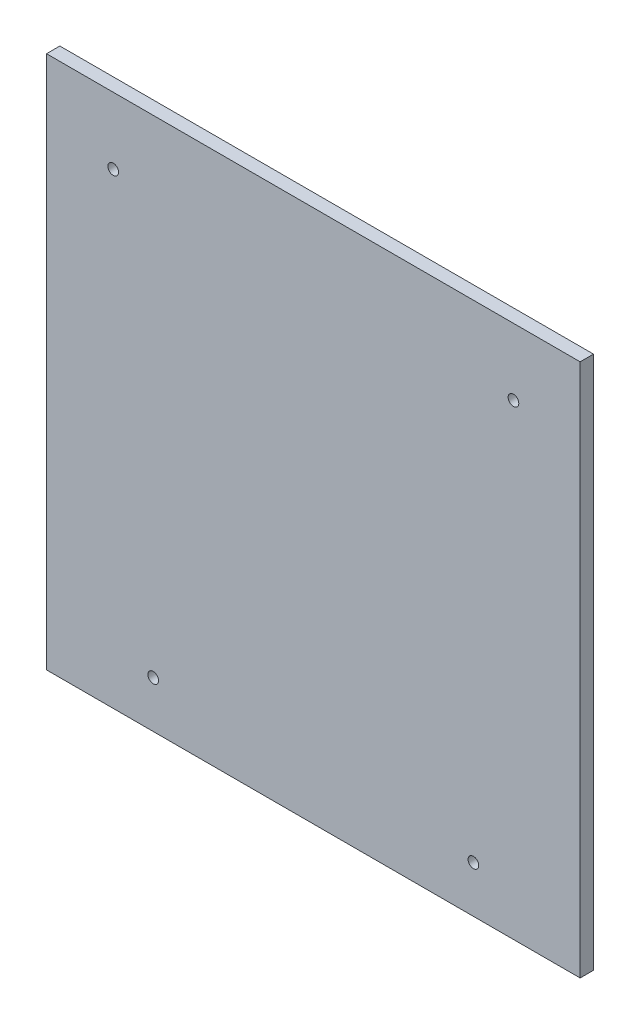
SolidWorks part; units mm, degrees
ref_plane "Front Plane" through (0, 0, 0) normal (0, 0, 1) x (1, 0, 0)
ref_plane "Top Plane" through (0, 0, 0) normal (0, 1, 0) x (1, 0, 0)
ref_plane "Right Plane" through (0, 0, 0) normal (1, 0, 0) x (0, 0, -1)
sketch "Sketch1" plane through (0, 0, 0) normal (0, 0, 1) x (1, 0, 0)
  line L0 (0, 0) -> (0, 238.5046) construction
  line L1 (-100, 100) -> (100, 100)
  line L2 (-100, 100) -> (-100, -100)
  line L3 (-100, -100) -> (100, -100)
  line L4 (100, 100) -> (100, -100)
  line L5 (-100, 100) -> (100, -100) construction
  line L6 (-100, -100) -> (100, 100) construction
  circle A0 centre (-60, -82.5) radius 2
  circle A1 centre (-75, 75) radius 2
  circle A2 centre (60, -82.5) radius 2
  circle A3 centre (75, 75) radius 2
  point P0 (0, 0)
  dimension "D3" = 4
  dimension "D4" = 4
  dimension "D1" = 200
  dimension "D2" = 200
  dimension "D5" = 60
  dimension "D6" = 82.5
  dimension "D7" = 75
  dimension "D8" = 75
extrude "Boss-Extrude1" add sketch "Sketch1" along normal blind 5
